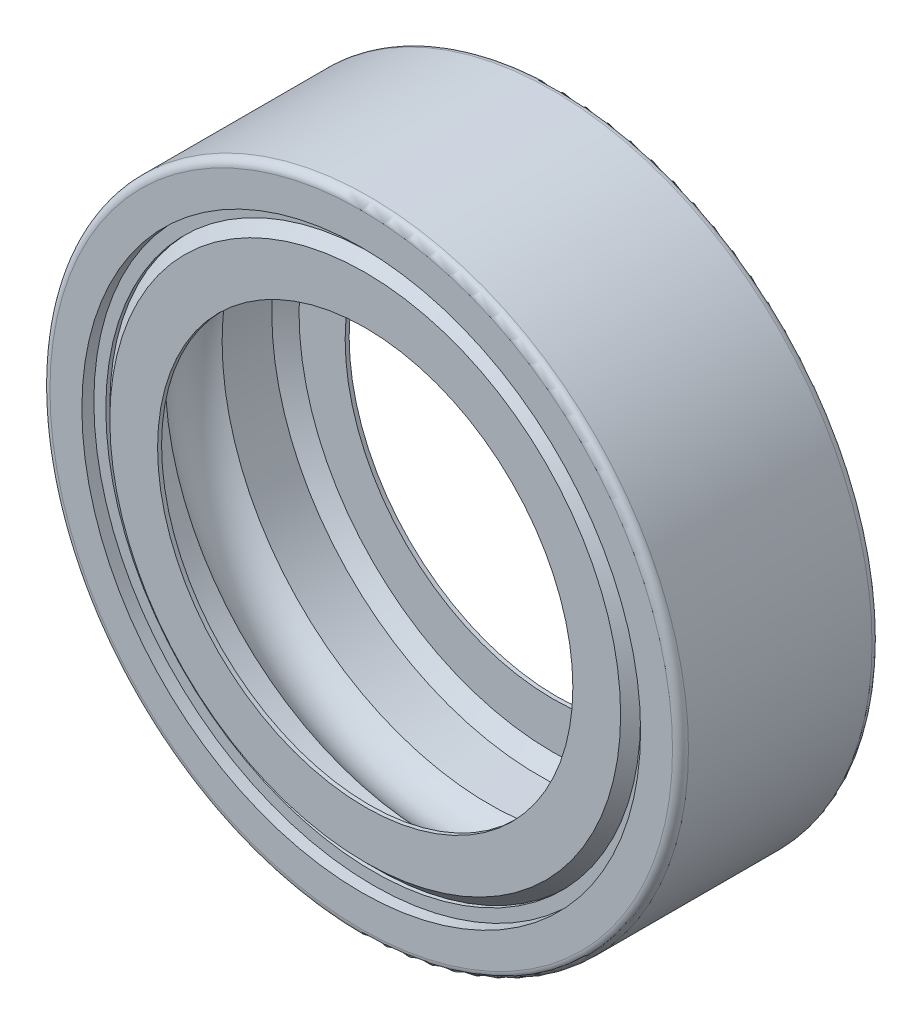
SolidWorks part; units mm, degrees
material "AISI 316 Stainless Steel Sheet (SS)"
ref_plane "Front Plane" through (0, 0, 0) normal (0, 0, 1) x (1, 0, 0)
ref_plane "Top Plane" through (0, 0, 0) normal (0, 1, 0) x (1, 0, 0)
ref_plane "Right Plane" through (0, 0, 0) normal (1, 0, 0) x (0, 0, -1)
sketch "Sketch1" plane through (0, 0, 0) normal (1, 0, 0) x (0, 0, -1)
  line L0 (-6.7554, 0) -> (6.7554, 0) construction
  line L1 (-2.5, 7) -> (-2.5, 7.8)
  line L2 (-2.2, 6.7) -> (-2.1, 6.7)
  line L3 (-2.3, 8) -> (2.3, 8)
  line L5 (-2.5, 6.7) -> (0, 7.35) construction
  line L6 (-2.5, 8) -> (0, 7.35) construction
  line L7 (-2.5, 4) -> (-2.5, 5.3) construction
  line L8 (-2.5, 4) -> (2.5, 4) construction
  line L9 (-2.5, 5.3) -> (2.5, 5.3) construction
  line L10 (2.5, 4) -> (2.5, 5.3) construction
  line L11 (-2.5, 4) -> (2.5, 5.3) construction
  line L12 (-2.5, 5.3) -> (2.5, 4) construction
  line L13 (0, 4.65) -> (0, 7.35) construction
  line L14 (-2.1, 6.7) -> (-2.4, 6.4)
  line L15 (-2.5, 7) -> (-2.2, 7)
  line L18 (-2.2, 7) -> (-2.2, 6.7)
  line L19 (-2.5, 6.7) -> (-2.2, 6.7) construction
  line L20 (-2.4, 6.4) -> (-2.4, 5.2029)
  line L21 (-2.4, 5.2029) -> (-2.3, 5.2029)
  line L22 (-2.3, 5.2029) -> (-2.3, 6.3586)
  line L23 (-2.3, 6.3586) -> (-1.9586, 6.7)
  line L24 (0, 4.65) -> (0, 0) construction
  line L25 (-1.9586, 6.7) -> (-0.7141, 6.7)
  line L26 (-2.5, 6.7) -> (-2.5, 7) construction
  line L28 (2.5, 6.7) -> (2.5, 7) construction
  line L29 (2.5, 6.7) -> (2.2, 6.7) construction
  line L30 (2.5, 8) -> (0, 7.35) construction
  line L31 (2.5, 6.7) -> (0, 7.35) construction
  line L32 (2.3, 6.3586) -> (1.9586, 6.7)
  line L33 (2.3, 5.2029) -> (2.3, 6.3586)
  line L34 (2.4, 5.2029) -> (2.3, 5.2029)
  line L35 (2.4, 6.4) -> (2.4, 5.2029)
  line L36 (2.2, 7) -> (2.2, 6.7)
  line L37 (2.5, 7) -> (2.2, 7)
  line L38 (2.1, 6.7) -> (2.4, 6.4)
  line L39 (2.2, 6.7) -> (2.1, 6.7)
  line L40 (2.5, 7) -> (2.5, 7.8)
  line L41 (0.7141, 6.7) -> (1.9586, 6.7)
  circle A0 centre (0, 6) radius 1 construction
  arc A1 (-2.5, 7.8) -> (-2.3, 8) centre (-2.3, 7.8) cw
  arc A2 (2.5, 7.8) -> (2.3, 8) centre (2.3, 7.8) ccw
  arc A3 (-0.7141, 6.7) -> (0.7141, 6.7) centre (0, 6) cw
  point P3 (0, 7.35)
  point P4 (0, 0)
  point P12 (0, 4.65)
  point P45 (0, 7)
  dimension "D3" = 2
  dimension "D14" = 0.2
  dimension "D15" = 1
  dimension "D1" = 8
  dimension "D2" = 5
  dimension "D4" = 5
  dimension "D5" = 4
  dimension "D6" = 1.3
  dimension "D7" = 0.3
  dimension "D8" = 0.3
  dimension "D9" = 45
  dimension "D10" = 0.1
  dimension "D11" = 0.1
  dimension "D12" = 0.1
  dimension "D13" = 0.1
revolve "Revolve1" add sketch "Sketch1" angle 360 about L0
